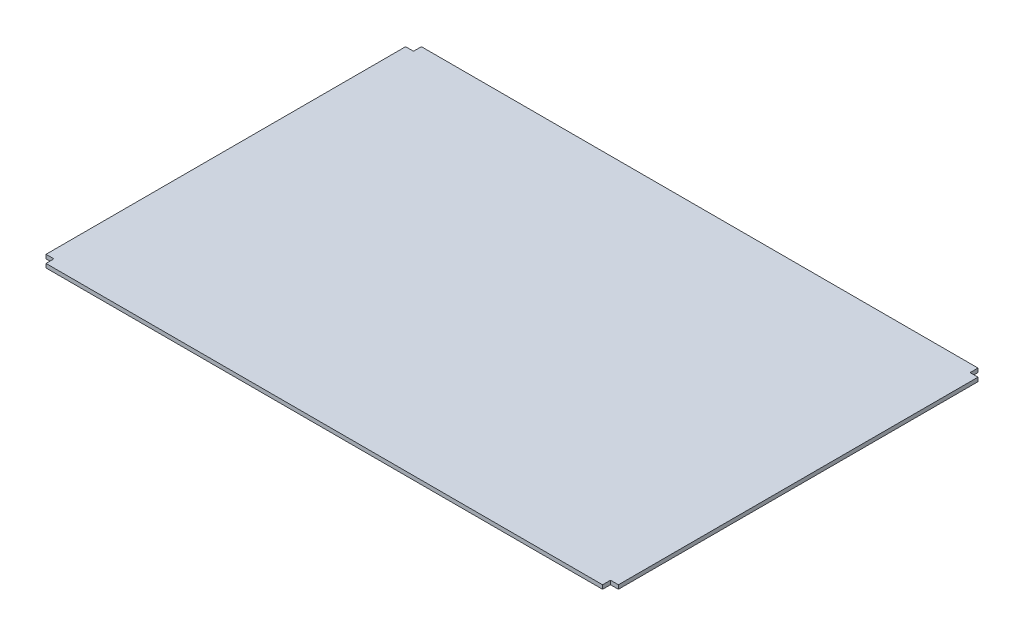
SolidWorks part; units mm, degrees
ref_plane "Piano frontale" through (0, 0, 0) normal (0, 0, 1) x (1, 0, 0)
ref_plane "Piano superiore" through (0, 0, 0) normal (0, 1, 0) x (1, 0, 0)
ref_plane "Piano destro" through (0, 0, 0) normal (1, 0, 0) x (0, 0, -1)
sketch "Schizzo1" plane through (0, 0, 0) normal (0, 1, 0) x (1, 0, 0)
  line L1 (1388.5, -910) -> (-1428.5, -910)
  line L2 (1428.5, -870) -> (1428.5, 950)
  line L3 (1388.5, 990) -> (-1428.5, 990)
  line L4 (-1468.5, -870) -> (-1468.5, 950)
  line L7 (1428.5, -870) -> (1388.5, -870)
  line L8 (1388.5, -910) -> (1388.5, -870)
  line L9 (1428.5, 950) -> (1388.5, 950)
  line L10 (1388.5, 990) -> (1388.5, 950)
  line L11 (-1468.5, 950) -> (-1428.5, 950)
  line L12 (-1428.5, 990) -> (-1428.5, 950)
  line L13 (-1468.5, -870) -> (-1428.5, -870)
  line L14 (-1428.5, -910) -> (-1428.5, -870)
extrude "Estrusione-Estrusione1" add sketch "Schizzo1" along normal blind 20
